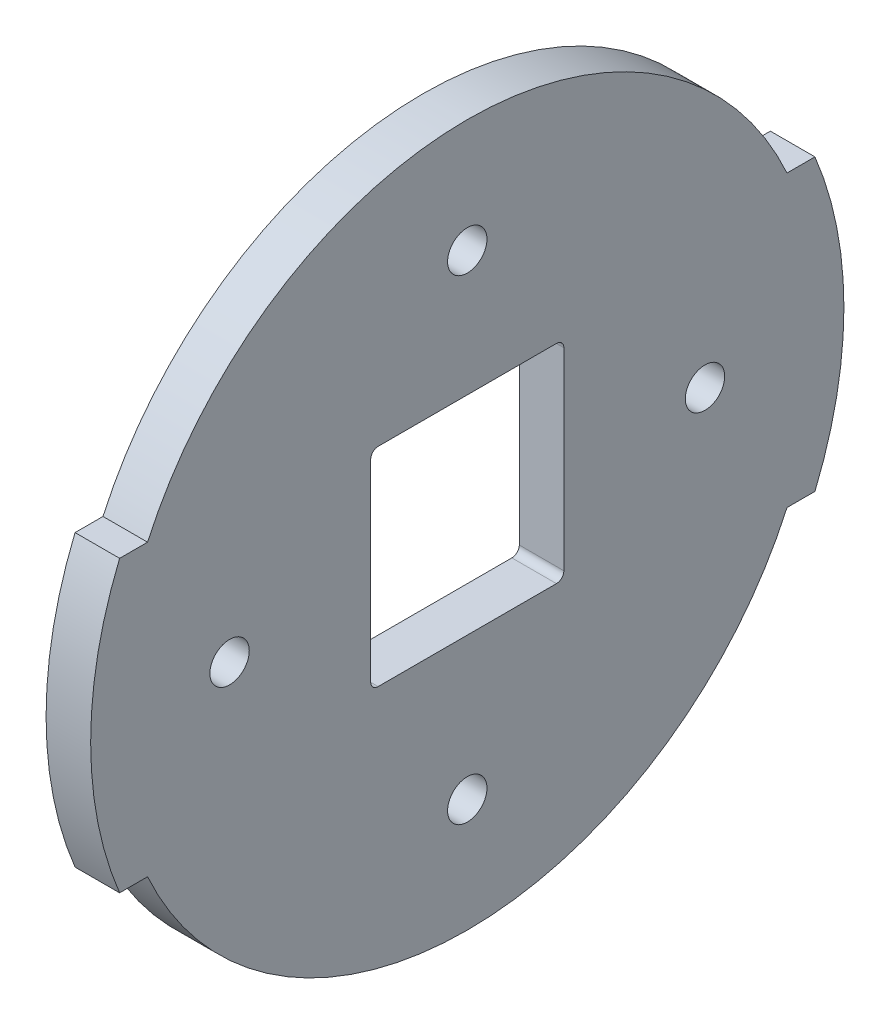
SolidWorks part; units mm, degrees
material "Perspex (TM) GS Acrylic Cast Sheet"
ref_plane "Front Plane" through (0, 0, 0) normal (0, 0, 1) x (1, 0, 0)
ref_plane "Top Plane" through (0, 0, 0) normal (0, 1, 0) x (1, 0, 0)
ref_plane "Right Plane" through (0, 0, 0) normal (1, 0, 0) x (0, 0, -1)
sketch "Sketch1" plane through (0, 0, 0) normal (1, 0, 0) x (0, 0, -1)
  line L0 (-46.8, 19.5) -> (-43.0385, 19.5)
  line L3 (-46.8, -19.5) -> (-43.0385, -19.5)
  line L4 (46.8, -19.5) -> (43.0385, -19.5)
  line L5 (46.8, 19.5) -> (43.0385, 19.5)
  arc A0 (-43.0385, -19.5) -> (43.0385, -19.5) centre (0, 0) ccw
  arc A1 (-46.8, 19.5) -> (-46.8, -19.5) centre (0, 0) ccw
  arc A2 (46.8, -19.5) -> (46.8, 19.5) centre (0, 0) ccw
  arc A3 (43.0385, 19.5) -> (-43.0385, 19.5) centre (0, 0) ccw
  dimension "D1" = 101.4
  dimension "D2" = 94.5
  dimension "D3" = 19.5
  dimension "D4" = 39
  dimension "D5" = 19.5
  dimension "D6" = 39
extrude "Boss-Extrude1" add sketch "Sketch1" along normal blind 6
sketch "Sketch2" plane through (6, 0, 0) normal (1, 0, 0) x (0, 0, -1)
  line L0 (12, -12.85) -> (-12, -12.85)
  line L1 (13, -3.85) -> (13, -11.85)
  line L2 (12, -11.85) -> (-12, -11.85)
  line L3 (-13, -11.85) -> (-13, -3.85)
  line L4 (-13, -3.85) -> (-13, 14.15)
  line L5 (13, -3.85) -> (13, 14.15)
  line L6 (12, 15.15) -> (-12, 15.15)
  line L7 (12, -12.85) -> (-12, -12.85) construction
  arc A0 (-13, -11.85) -> (-12, -12.85) centre (-12, -11.85) ccw
  arc A1 (13, -11.85) -> (12, -12.85) centre (12, -11.85) cw
  arc A4 (12, -11.85) -> (13, -10.85) centre (12, -10.85) ccw
  arc A5 (-13, -10.85) -> (-12, -11.85) centre (-12, -10.85) ccw
  arc A8 (-13, 14.15) -> (-12, 15.15) centre (-12, 14.15) cw
  arc A9 (13, 14.15) -> (12, 15.15) centre (12, 14.15) ccw
  point P26 (13, 15.15)
  dimension "D2" = 1
  dimension "D4" = 1
  dimension "D1" = 19
  dimension "D3" = 1
extrude "Cut-Extrude1" cut sketch "Sketch2" against normal blind 20 contours L5 A9 L6 A8 L4 L3 A5 L2 A4 L1 | A5 L3 A0 L0 A1 L1 A4 L2
sketch "Sketch3" plane through (6, 0, 0) normal (1, 0, 0) x (0, 0, -1)
  line L0 (0, 0) -> (-33.4108, 33.4108)
  line L1 (-33.4108, 33.4108) -> (33.4108, -33.4108)
  line L2 (0, 0) -> (33.4108, 33.4108)
  line L3 (0, 0) -> (-33.4108, -33.4108)
  circle A0 centre (0, 0) radius 47.25 construction
ref_plane "Plane1" through (0, 33.4108, 33.4108) normal (0, 0.7071, 0.7071) x (-1, 0, 0)
ref_plane "Plane2" through (0, -33.4108, 33.4108) normal (0, -0.7071, 0.7071) x (-1, 0, 0)
ref_plane "Plane3" through (0, 33.4108, -33.4108) normal (0, 0.7071, -0.7071) x (-1, 0, 0)
ref_plane "Plane4" through (0, -33.4108, -33.4108) normal (0, -0.7071, -0.7071) x (-1, 0, 0)
hole_wizard "M5 Clearance Hole1" positions "Sketch15" profile "Sketch14" hole size "M5" standard "ISO"
sketch "Sketch15" plane through (0, 0, 0) normal (-1, 0, 0) x (0, 0, 1)
  point P0 (-32, 0)
  point P8 (0, 32)
  point P9 (32, 0)
  point P10 (0, -32)
  dimension "D2" = 4
sketch "Sketch14" plane through (0, 0, -32) normal (0, 1, 0) x (0, 0, 1)
  line L0 (0, 0) -> (0, 16.5923)
  line L1 (0, 16.5923) -> (2.65, 15)
  line L2 (2.65, 15) -> (2.65, 0)
  line L5 (2.65, 0) -> (0, 0)
  line L10 (0, 16.5923) -> (-2.65, 15) construction
  line L11 (0, -6.35) -> (0, 107.95) construction
  dimension "Hole Dia." = 5.3
  dimension "Hole Depth" = 15
  dimension "Drill Angle" = 118
sketch "Sketch16" plane through (6, 0, 0) normal (1, 0, 0) x (0, 0, -1)
  line L0 (12, 15.15) -> (-12, 15.15) construction
  line L1 (19, 15.15) -> (-19, 15.15)
  line L2 (0, 15.15) -> (0, -4.85)
  line L3 (19, -4.85) -> (-19, -4.85)
  line L4 (-19, 15.15) -> (-19, -4.85)
  line L5 (19, 15.15) -> (19, -4.85)
  line M5 (13, 14.15) -> (13, -11.85)
  line M9 (-13, -11.85) -> (-13, 14.15)
  arc M10 (-13, 14.15) -> (-12, 15.15) centre (-12, 14.15) cw
  line M11 (-12, 15.15) -> (12, 15.15)
  arc M12 (12, 15.15) -> (13, 14.15) centre (12, 14.15) cw
  dimension "D1" = 20
  dimension "D2" = 19
extrude "Cut-Extrude2" [suppressed] cut sketch "Sketch16" against normal blind 1.5 contours L1 L4 L3 M9 M10 | L3 L2 M11 M10 M9 | L3 L1 L2 M5 M12 | L5 L1 L3 M12 M5
fillet "Fillet1" [suppressed] radius 1
